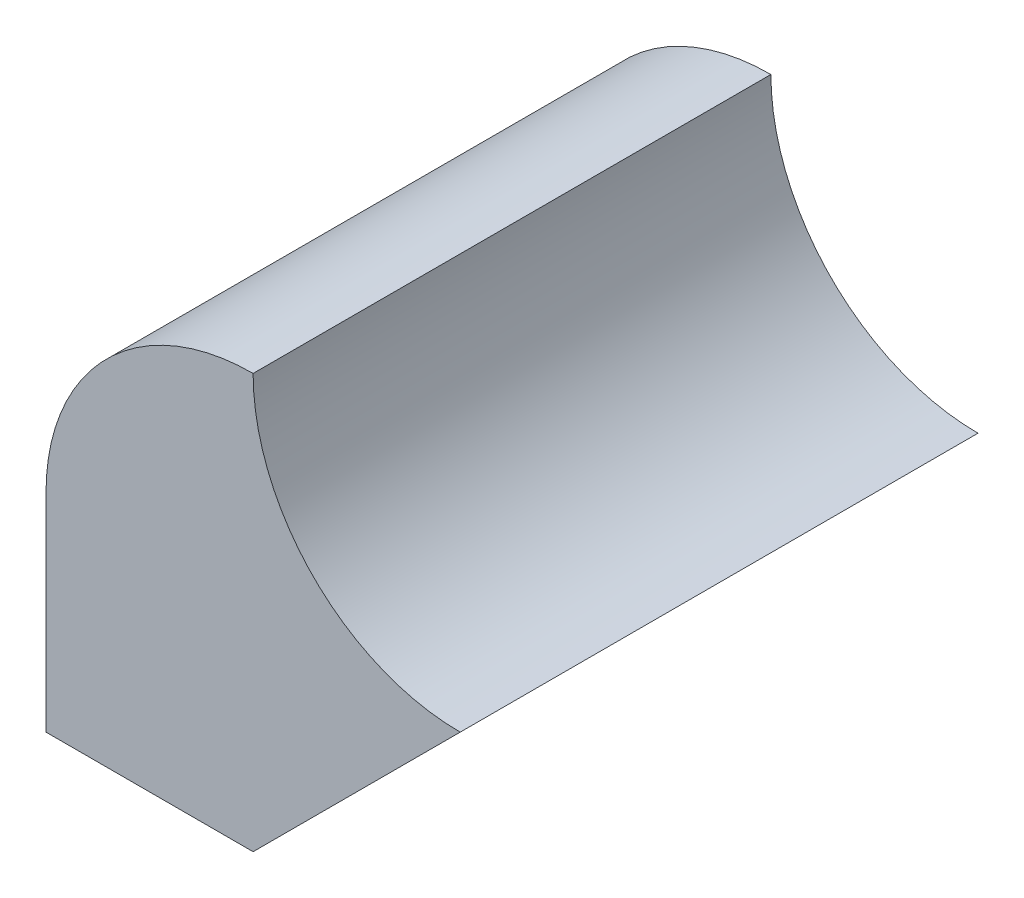
SolidWorks part; units mm, degrees
ref_plane "Front Plane" through (0, 0, 0) normal (0, 0, 1) x (1, 0, 0)
ref_plane "Top Plane" through (0, 0, 0) normal (0, 1, 0) x (1, 0, 0)
ref_plane "Right Plane" through (0, 0, 0) normal (1, 0, 0) x (0, 0, -1)
sketch "Sketch1" plane through (0, 0, 0) normal (0, 0, 1) x (1, 0, 0)
  line L0 (-20, 0) -> (-20, -10)
  line L1 (-20, -10) -> (-10, -10)
  line L2 (-10, -10) -> (0, 0)
  arc A0 (-20, 0) -> (-10, 10) centre (-10, 0) cw
  arc A1 (-10, 10) -> (0, 0) centre (0, 10) ccw
  dimension "D4" = 10
  dimension "D1" = 10
  dimension "D2" = 10
  dimension "D3" = 10
extrude "Boss-Extrude1" add sketch "Sketch1" along normal blind 25
